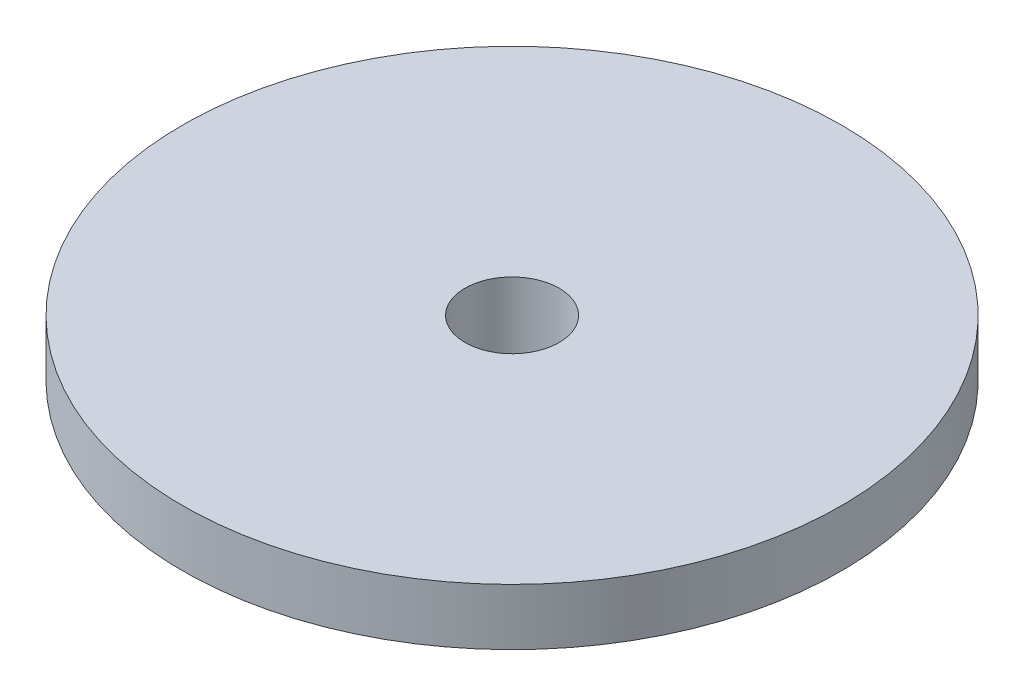
SolidWorks part; units mm, degrees
ref_plane "Front Plane" through (0, 0, 0) normal (0, 0, 1) x (1, 0, 0)
ref_plane "Top Plane" through (0, 0, 0) normal (0, 1, 0) x (1, 0, 0)
ref_plane "Right Plane" through (0, 0, 0) normal (1, 0, 0) x (0, 0, -1)
sketch "Sketch1" plane through (0, 0, 0) normal (0, 0, 1) x (1, 0, 0)
  line L0 (0, 0) -> (0, 10)
  line L1 (0, 10) -> (17.5, 10)
  line L2 (17.5, 10) -> (17.5, 7)
  line L4 (7, 0) -> (0, 0)
  line L5 (17.5, 7) -> (7, 0)
  dimension "D1" = 17.5
  dimension "D2" = 7
  dimension "D3" = 3
  dimension "D4" = 10
revolve "Revolve1" add sketch "Sketch1" angle 360 about L0
sketch "Sketch4" plane through (0, 0, 0) normal (0, -1, 0) x (-1, 0, 0)
  point P0 (0, 0)
sketch "Sketch10" plane through (0, 0, 0) normal (0, -1, 0) x (1, 0, 0)
  circle A0 centre (0, 0) radius 2.5
  dimension "D1" = 5
extrude "Cut-Extrude1" cut sketch "Sketch10" against normal through all
sketch "Sketch11" plane through (0, 0, 0) normal (0, -1, 0) x (1, 0, 0)
  circle A0 centre (0, 0) radius 4.5
  dimension "D1" = 9
extrude "Cut-Extrude2" cut sketch "Sketch11" against normal blind 5 contours A0
